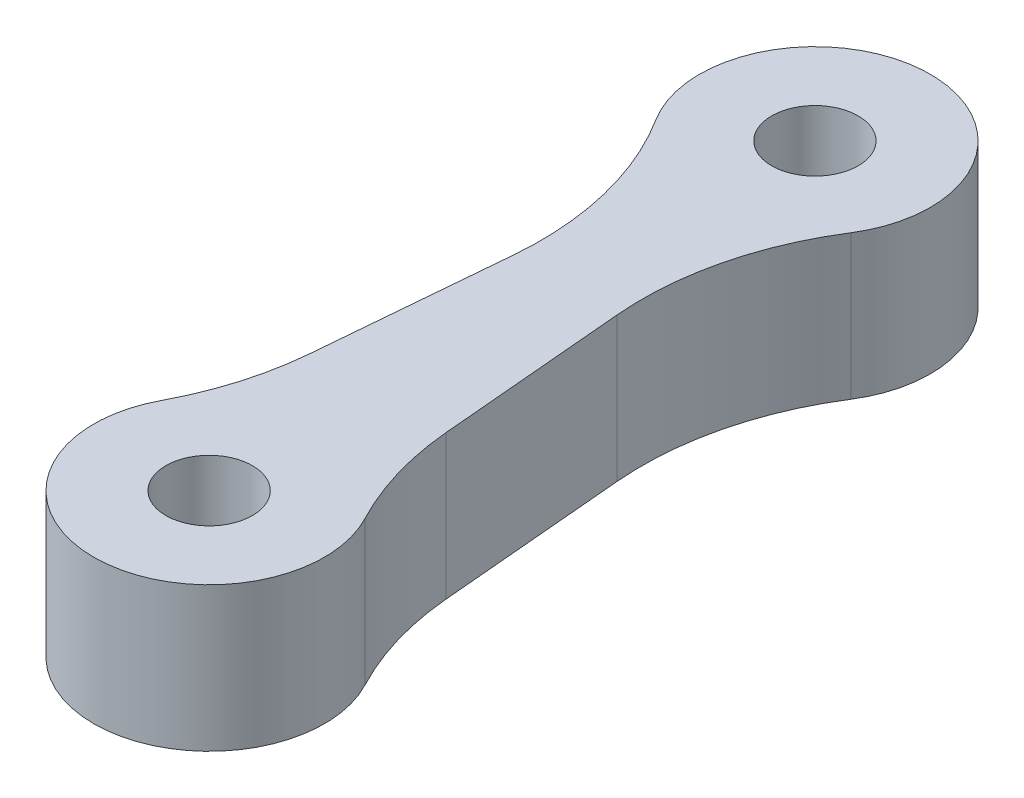
SolidWorks part; units mm, degrees
ref_plane "Спереди" through (0, 0, 0) normal (0, 0, 1) x (1, 0, 0)
ref_plane "Сверху" through (0, 0, 0) normal (0, 1, 0) x (1, 0, 0)
ref_plane "Справа" through (0, 0, 0) normal (1, 0, 0) x (0, 0, -1)
sketch "Эскиз1" plane through (0, 0, 0) normal (0, 1, 0) x (1, 0, 0)
  line L0 (0, 0) -> (0, -33.9933) construction
  line L3 (0, 0) -> (0, 39.5512) construction
  line L10 (3.5941, -17.3239) -> (4.7292, -30.2984)
  line L13 (-3.5941, -17.3239) -> (-4.7292, -30.2984)
  circle A0 centre (0, 0) radius 3
  circle A1 centre (0, 0) radius 50
  circle A2 centre (0, -42) radius 3
  arc A3 (-3.5941, -17.3239) -> (-6.7625, -4.2741) centre (-24.5142, -15.4937) ccw
  arc A4 (6.7625, -4.2741) -> (-6.7625, -4.2741) centre (0, 0) ccw
  circle A5 centre (0, 0) radius 8 construction
  arc A6 (3.5941, -17.3239) -> (6.7625, -4.2741) centre (24.5142, -15.4937) cw
  arc A7 (-7.0757, -38.2671) -> (7.0757, -38.2671) centre (0, -42) ccw
  circle A9 centre (0, -42) radius 8 construction
  arc A41 (7.0156, 49.5054) -> (-7.0156, 49.5054) centre (0, 0) ccw
  arc A49 (-7.0757, -38.2671) -> (-4.7292, -30.2984) centre (-25.6493, -28.4681) ccw
  arc A50 (7.0757, -38.2671) -> (4.7292, -30.2984) centre (25.6493, -28.4681) cw
  point P6 (0, 0)
  point P8 (8, 0)
  point P17 (0, 8)
  point P18 (45, 0)
  point P22 (8, -42)
  point P61 (8, -42)
  point P98 (0, 0)
  point P106 (0, -42)
  point P115 (-5.2228, -35.9401)
  dimension "D1" = 6
  dimension "D2" = 21
  dimension "D14" = 21
  dimension "D4" = 21
  dimension "D3" = 5
  dimension "D5" = 5
extrude "Бобышка-Вытянуть1" add sketch "Эскиз1" along normal blind 10 contours A7 A50 L10 A6 A4 A3 L13 A49 A2 A0
